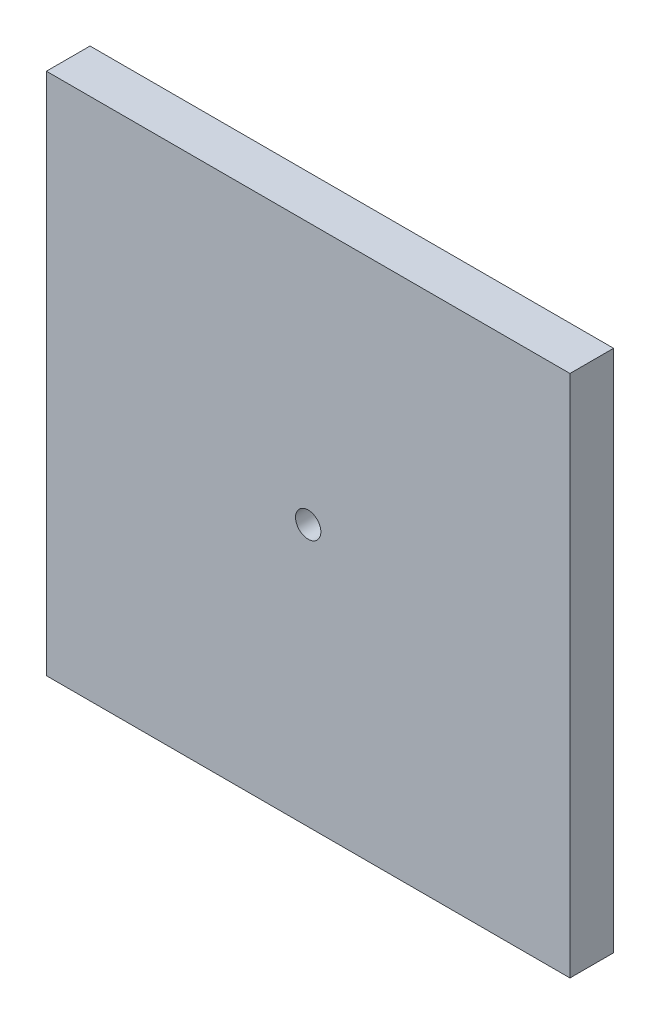
SolidWorks part; units mm, degrees
ref_plane "Front" through (0, 0, 0) normal (0, 0, 1) x (1, 0, 0)
ref_plane "Top" through (0, 0, 0) normal (0, 1, 0) x (1, 0, 0)
ref_plane "Right" through (0, 0, 0) normal (1, 0, 0) x (0, 0, -1)
sketch "Sketch1" plane through (0, 0, 0) normal (0, 0, 1) x (1, 0, 0)
  line L0 (38.1, 76.2) -> (38.1, 0) construction
  line L1 (0, 0) -> (76.2, 0)
  line L2 (0, 0) -> (0, 76.2)
  line L3 (0, 76.2) -> (76.2, 76.2)
  line L4 (76.2, 0) -> (76.2, 76.2)
  line L5 (0, 38.1) -> (76.2, 38.1) construction
  circle A0 centre (38.1, 38.1) radius 1.8415
  dimension "D3" = 3.683
  dimension "D1" = 76.2
  dimension "D2" = 76.2
extrude "Boss-Extrude1" add sketch "Sketch1" along normal blind 6.35
